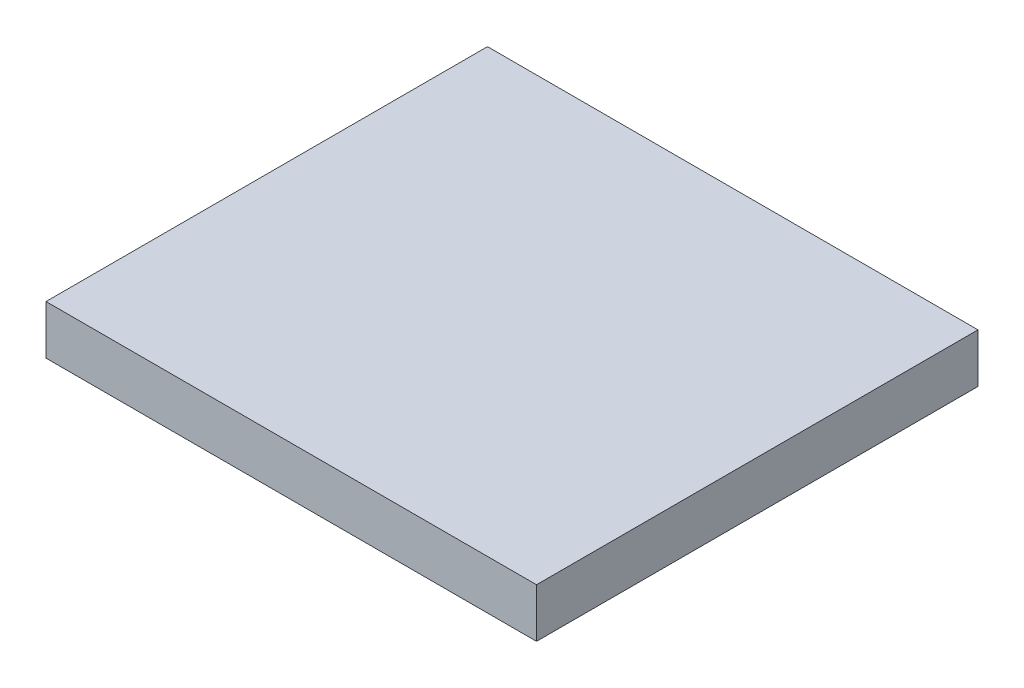
SolidWorks part; units mm, degrees
ref_plane "Front Plane" through (0, 0, 0) normal (0, 0, 1) x (1, 0, 0)
ref_plane "Top Plane" through (0, 0, 0) normal (0, 1, 0) x (1, 0, 0)
ref_plane "Right Plane" through (0, 0, 0) normal (1, 0, 0) x (0, 0, -1)
sketch "Sketch1" plane through (0, 0, 0) normal (0, 1, 0) x (1, 0, 0)
  line L1 (-50, 45) -> (50, 45)
  line L2 (-50, 45) -> (-50, -45)
  line L3 (-50, -45) -> (50, -45)
  line L4 (50, 45) -> (50, -45)
  line L5 (-50, 45) -> (50, -45) construction
  line L6 (-50, -45) -> (50, 45) construction
  point P0 (0, 0)
  dimension "D1" = 100
  dimension "D2" = 90
extrude "Boss-Extrude1" add sketch "Sketch1" along normal blind 10
